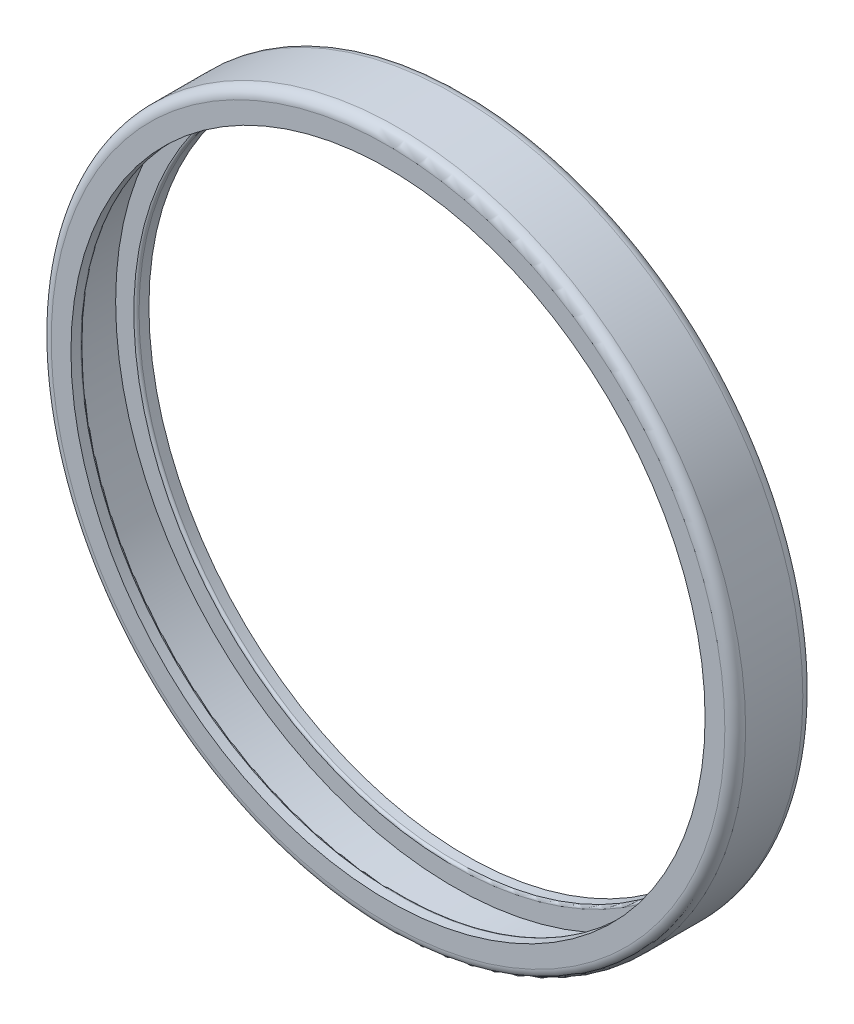
SolidWorks part; units mm, degrees
ref_plane "Front Plane" through (0, 0, 0) normal (0, 0, 1) x (1, 0, 0)
ref_plane "Top Plane" through (0, 0, 0) normal (0, 1, 0) x (1, 0, 0)
ref_plane "Right Plane" through (0, 0, 0) normal (1, 0, 0) x (0, 0, -1)
sketch "Sketch1" plane through (0, 0, 0) normal (1, 0, 0) x (0, 0, -1)
  line L0 (25, 0) -> (-25, 0) construction
  line L1 (-3.75, 33.4) -> (3.75, 33.4)
  line L2 (-3.75, 33.4) -> (-3.75, 30.5)
  line L3 (-3.75, 30.5) -> (-2.55, 30.5)
  line L4 (3.75, 33.4) -> (3.75, 30.5)
  line L5 (-2.55, 30.5) -> (-2.55, 32.5)
  line L6 (-2.55, 32.5) -> (2.55, 32.5)
  line L7 (2.55, 32.5) -> (2.55, 30.5)
  line L8 (2.55, 30.5) -> (3.75, 30.5)
  dimension "D1" = 50
  dimension "D2" = 33.4
  dimension "D3" = 2.9
  dimension "D4" = 7.5
  dimension "D5" = 3.75
  dimension "D6" = 5.1
  dimension "D7" = 2.55
  dimension "D8" = 2
revolve "Revolve1" add sketch "Sketch1" angle 360 about L0
fillet "Fillet2" radius 0.25 2 edges at (-30.5, 0, 2.55) (-30.5, 0, -2.55)
fillet "Fillet3" radius 1 2 edges at (-33.4, 0, -3.75) (-33.4, 0, 3.75)
